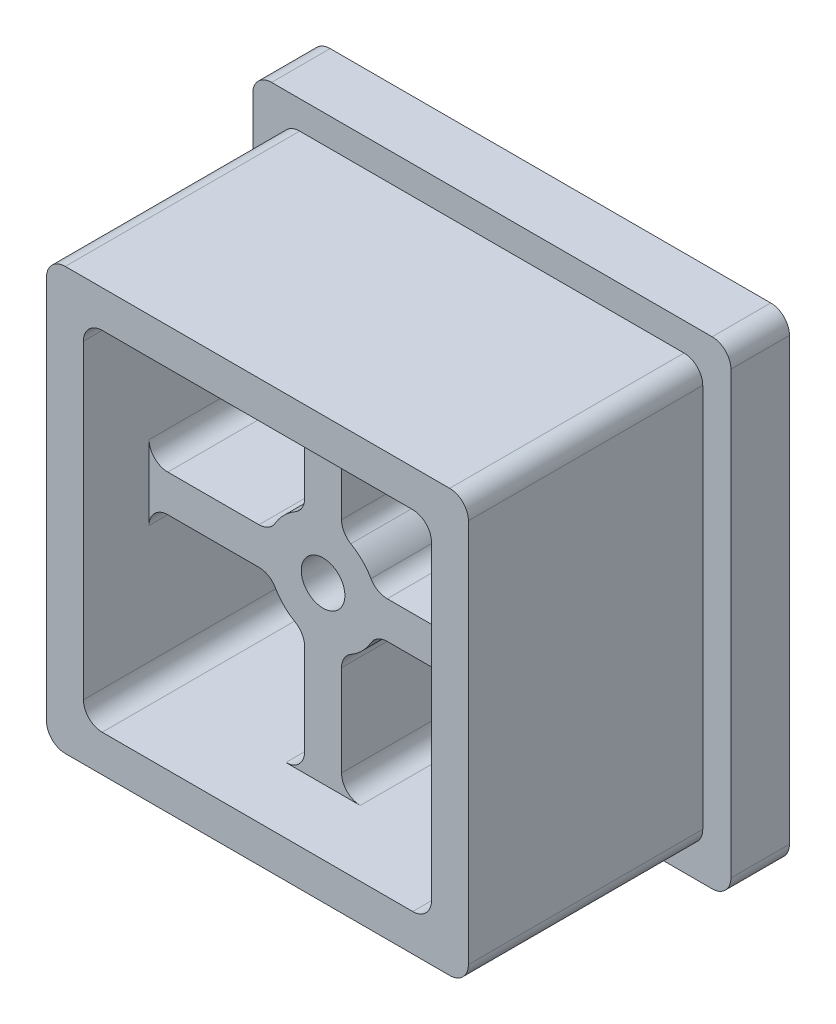
SolidWorks part; units mm, degrees
material "Nylon 101"
ref_plane "Front Plane" through (0, 0, 0) normal (0, 0, 1) x (1, 0, 0)
ref_plane "Top Plane" through (0, 0, 0) normal (0, 1, 0) x (1, 0, 0)
ref_plane "Right Plane" through (0, 0, 0) normal (1, 0, 0) x (0, 0, -1)
sketch "Sketch1" plane through (0, 0, 0) normal (0, 0, 1) x (1, 0, 0)
  line L1 (-5.715, 5.715) -> (5.715, 5.715)
  line L2 (-5.715, 5.715) -> (-5.715, -5.715)
  line L3 (-5.715, -5.715) -> (5.715, -5.715)
  line L4 (5.715, 5.715) -> (5.715, -5.715)
  line L5 (-5.715, 5.715) -> (5.715, -5.715) construction
  line L6 (-5.715, -5.715) -> (5.715, 5.715) construction
  point P0 (0, 0)
  dimension "D1" = 11.43
  dimension "D2" = 11.43
extrude "Boss-Extrude1" add sketch "Sketch1" along normal blind 4.7625 and the other way blind 1.5875
sketch "Sketch2" plane through (0, 0, -1.5875) normal (0, 0, -1) x (-1, 0, 0)
  line L0 (-6.477, 6.477) -> (-6.477, -6.477)
  line L1 (-6.477, -6.477) -> (6.477, -6.477)
  line L2 (6.477, -6.477) -> (6.477, 6.477)
  line L3 (6.477, 6.477) -> (-6.477, 6.477)
  line L4 (-5.715, 5.715) -> (-5.715, -5.715)
  line L5 (-5.715, -5.715) -> (5.715, -5.715)
  line L6 (5.715, -5.715) -> (5.715, 5.715)
  line L7 (5.715, 5.715) -> (-5.715, 5.715)
  line L8 (-5.715, 5.715) -> (-5.715, -5.715) construction
  line L9 (-5.715, -5.715) -> (5.715, -5.715) construction
  line L10 (5.715, -5.715) -> (5.715, 5.715) construction
  line L11 (5.715, 5.715) -> (-5.715, 5.715) construction
  dimension "D1" = 0
  dimension "D2" = 0.762
extrude "Boss-Extrude2" add sketch "Sketch2" along normal blind 1.5875
sketch "Sketch3" plane through (0, 0, 4.7625) normal (0, 0, 1) x (1, 0, 0)
  line L0 (5.207, -5.207) -> (5.207, 5.207)
  line L1 (5.207, 5.207) -> (-5.207, 5.207)
  line L2 (-5.207, 5.207) -> (-5.207, -5.207)
  line L3 (-5.207, -5.207) -> (5.207, -5.207)
  line L4 (5.715, -5.715) -> (5.715, 5.715)
  line L5 (5.715, 5.715) -> (-5.715, 5.715)
  line L6 (-5.715, 5.715) -> (-5.715, -5.715)
  line L7 (-5.715, -5.715) -> (5.715, -5.715)
  line L8 (5.715, -5.715) -> (5.715, 5.715) construction
  line L9 (5.715, 5.715) -> (-5.715, 5.715) construction
  line L10 (-5.715, 5.715) -> (-5.715, -5.715) construction
  line L11 (-5.715, -5.715) -> (5.715, -5.715) construction
  dimension "D1" = 0
  dimension "D2" = 0.508
extrude "Cut-Extrude1" [suppressed] cut sketch "Sketch3" against normal blind 1.8415
sketch "Sketch6" plane through (0, 0, -3.175) normal (0, 0, -1) x (-1, 0, 0)
  line L0 (-6.477, 6.477) -> (6.477, -6.477) construction
  line L2 (1.27, -1.27) -> (-1.27, -1.27)
  line L3 (1.27, -1.27) -> (1.27, 1.27)
  line L4 (1.27, 1.27) -> (-1.27, 1.27)
  line L5 (-1.27, -1.27) -> (-1.27, 1.27)
  line L6 (1.27, -1.27) -> (-1.27, 1.27) construction
  line L7 (1.27, 1.27) -> (-1.27, -1.27) construction
  point P4 (0, 0)
  dimension "D1" = 2.54
  dimension "D2" = 2.54
sketch "Sketch7" [suppressed] plane through (0, 0, 2.921) normal (0, 0, 1) x (1, 0, 0)
  line L0 (7.3025, 7.3025) -> (-7.3025, -7.3025) construction
  line L1 (4.445, -4.445) -> (-4.445, -4.445)
  line L2 (4.445, -4.445) -> (4.445, 4.445)
  line L3 (4.445, 4.445) -> (-4.445, 4.445)
  line L4 (-4.445, -4.445) -> (-4.445, 4.445)
  line L5 (4.445, -4.445) -> (-4.445, 4.445) construction
  line L6 (4.445, 4.445) -> (-4.445, -4.445) construction
  line L7 (-5.207, 5.207) -> (-5.207, -5.207) construction
  line L8 (5.207, 5.207) -> (-5.207, 5.207) construction
  point P0 (0, 0)
  dimension "D1" = 0.762
  dimension "D2" = 0.762
loft "Cut-Loft1" [suppressed] cut profiles "Sketch7", "Sketch6"
fillet "Fillet1" [suppressed] radius 0.508
sketch "Sketch8" [suppressed] plane through (0, 0, 0) normal (1, 0, 0) x (0, 0, -1)
  line L0 (-4.7625, -5.207) -> (-4.7625, -5.715) construction
  line L1 (-4.7625, -5.207) -> (1.5875, -5.207) construction
  line L2 (1.5875, -5.715) -> (-4.7625, -5.715) construction
  line L3 (-4.5085, -5.207) -> (-4.7625, -5.207)
  line L4 (-4.7625, -5.207) -> (-4.7625, -5.715) construction
  line L5 (-4.7625, -5.715) -> (-4.5085, -5.715)
  line L6 (-4.7625, -5.207) -> (-4.7879, -5.207)
  line L7 (-4.7879, -5.207) -> (-4.7879, -5.715)
  line L8 (-4.7879, -5.715) -> (-4.7625, -5.715)
  arc A0 (-4.5085, -5.207) -> (-4.5085, -5.715) centre (-4.5085, -5.461) ccw
  dimension "D1" = 0.0254
sketch "Sketch9" plane through (0, 0, 4.7625) normal (0, 0, 1) x (1, 0, 0)
  line L4 (5.715, 5.715) -> (-5.715, 5.715)
  line L5 (-5.715, 5.715) -> (-5.715, -5.715)
  line L6 (-5.715, -5.715) -> (5.715, -5.715)
  line L7 (5.715, -5.715) -> (5.715, 5.715)
  line L8 (5.715, 5.715) -> (-5.715, 5.715)
  line L9 (-5.715, 5.715) -> (-5.715, -5.715)
  line L10 (-5.715, -5.715) -> (5.715, -5.715)
  line L11 (5.715, -5.715) -> (5.715, 5.715)
  dimension "D1" = 0
sweep "Cut-Sweep2" [suppressed] cut profiles "Sketch8" path "Sketch9"
sketch "Sketch10" [suppressed] plane through (0, 0, 2.921) normal (0, 0, 1) x (1, 0, 0)
  line L0 (-4.3153, 3.8458) -> (-4.3153, -3.8458) construction
  line L1 (-4.3153, -3.8458) -> (-1.27, -0.8005) construction
  line L2 (-1.27, -0.8005) -> (-1.27, 0.8005) construction
  line L3 (-1.27, 0.8005) -> (-4.3153, 3.8458) construction
  line L4 (-0.8005, 1.27) -> (0.8005, 1.27) construction
  line L5 (0.8005, 1.27) -> (3.8458, 4.3153) construction
  line L6 (3.8458, 4.3153) -> (-3.8458, 4.3153) construction
  line L7 (-3.8458, 4.3153) -> (-0.8005, 1.27) construction
  line L8 (1.27, 0.8005) -> (1.27, -0.8005) construction
  line L9 (1.27, -0.8005) -> (4.3153, -3.8458) construction
  line L10 (4.3153, -3.8458) -> (4.3153, 3.8458) construction
  line L11 (4.3153, 3.8458) -> (1.27, 0.8005) construction
  line L12 (0.8005, -1.27) -> (-0.8005, -1.27) construction
  line L13 (-0.8005, -1.27) -> (-3.8458, -4.3153) construction
  line L14 (-3.8458, -4.3153) -> (3.8458, -4.3153) construction
  line L15 (3.8458, -4.3153) -> (0.8005, -1.27) construction
  line L16 (-4.3153, 3.8458) -> (-4.3153, -3.8458) construction
  line L17 (-4.3153, -3.8458) -> (-1.27, -0.8005) construction
  line L18 (-1.27, -0.8005) -> (-1.27, 0.8005) construction
  line L19 (-1.27, 0.8005) -> (-4.3153, 3.8458) construction
  line L20 (-0.8005, 1.27) -> (0.8005, 1.27) construction
  line L21 (0.8005, 1.27) -> (3.8458, 4.3153) construction
  line L22 (3.8458, 4.3153) -> (-3.8458, 4.3153) construction
  line L23 (-3.8458, 4.3153) -> (-0.8005, 1.27) construction
  line L24 (1.27, 0.8005) -> (1.27, -0.8005) construction
  line L25 (1.27, -0.8005) -> (4.3153, -3.8458) construction
  line L26 (4.3153, -3.8458) -> (4.3153, 3.8458) construction
  line L27 (4.3153, 3.8458) -> (1.27, 0.8005) construction
  line L28 (0.8005, -1.27) -> (-0.8005, -1.27) construction
  line L29 (-0.8005, -1.27) -> (-3.8458, -4.3153) construction
  line L30 (-3.8458, -4.3153) -> (3.8458, -4.3153) construction
  line L31 (3.8458, -4.3153) -> (0.8005, -1.27) construction
  line L32 (-3.5533, 2.0061) -> (-3.5533, -2.0061)
  line L33 (-3.5533, -2.0061) -> (-2.032, -0.4849)
  line L34 (-2.032, -0.4849) -> (-2.032, 0.4849)
  line L35 (-2.032, 0.4849) -> (-3.5533, 2.0061)
  line L36 (-0.4849, 2.032) -> (0.4849, 2.032)
  line L37 (0.4849, 2.032) -> (2.0061, 3.5533)
  line L38 (2.0061, 3.5533) -> (-2.0061, 3.5533)
  line L39 (-2.0061, 3.5533) -> (-0.4849, 2.032)
  line L40 (2.032, 0.4849) -> (2.032, -0.4849)
  line L41 (2.032, -0.4849) -> (3.5533, -2.0061)
  line L42 (3.5533, -2.0061) -> (3.5533, 2.0061)
  line L43 (3.5533, 2.0061) -> (2.032, 0.4849)
  line L44 (0.4849, -2.032) -> (-0.4849, -2.032)
  line L45 (-0.4849, -2.032) -> (-2.0061, -3.5533)
  line L46 (-2.0061, -3.5533) -> (2.0061, -3.5533)
  line L47 (2.0061, -3.5533) -> (0.4849, -2.032)
  dimension "D1" = 0.762
extrude "Cut-Extrude2" [suppressed] cut sketch "Sketch10" against normal offset from surface (6.4135 mm away) 1.27
fillet "Fillet4" [suppressed] radius 0.254
fillet "Fillet5" [suppressed] radius 0.254
sketch "Sketch11" [suppressed] plane through (0, 0, 2.921) normal (0, 0, 1) x (1, 0, 0)
  line L1 (2.54, -2.54) -> (-2.54, -2.54)
  line L2 (2.54, -2.54) -> (2.54, 2.54)
  line L3 (2.54, 2.54) -> (-2.54, 2.54)
  line L4 (-2.54, -2.54) -> (-2.54, 2.54)
  line L5 (2.54, -2.54) -> (-2.54, 2.54) construction
  line L6 (2.54, 2.54) -> (-2.54, -2.54) construction
  point P0 (0, 0)
  dimension "D1" = 5.08
  dimension "D2" = 5.08
extrude "Cut-Extrude3" [suppressed] cut sketch "Sketch11" against normal through all draft 5
sketch "Sketch12" [suppressed] plane through (0, 0, 2.921) normal (0, 0, 1) x (1, 0, 0)
  line L0 (-5.207, 0) -> (5.207, 0)
  line L1 (-5.207, 5.207) -> (-5.207, -5.207) construction
  line L2 (5.207, -5.207) -> (5.207, 5.207) construction
  line L3 (0, 5.207) -> (0, -5.207)
  line L4 (5.207, 5.207) -> (-5.207, 5.207) construction
  line L5 (-5.207, -5.207) -> (5.207, -5.207) construction
extrude "Cut-Extrude-Thin1" [suppressed] cut sketch "Sketch12" against normal offset from surface (6.4135 mm away) 1.27 thin
fillet "Fillet6" [suppressed] radius 0.508
sketch "Sketch13" [suppressed] plane through (0, 0, 0) normal (1, 0, 0) x (0, 0, -1)
  line L0 (1.5875, -5.715) -> (-4.7625, -5.715) construction
  line L1 (-2.921, -5.207) -> (-4.7625, -5.207) construction
  line L2 (-4.7625, -5.715) -> (-4.7625, 5.715) construction
  line L3 (-4.5085, -5.207) -> (-5.0165, -5.207)
  line L4 (-5.0165, -5.207) -> (-5.0165, -5.715)
  line L5 (-5.0165, -5.715) -> (-4.5085, -5.715)
  arc A0 (-4.5085, -5.207) -> (-4.5085, -5.715) centre (-4.5085, -5.461) ccw
  dimension "D1" = 0.508
sketch "Sketch14" plane through (0, 0, 4.7625) normal (0, 0, 1) x (1, 0, 0)
  line L4 (5.715, -5.715) -> (5.715, 5.715)
  line L5 (5.715, 5.715) -> (-5.715, 5.715)
  line L6 (-5.715, 5.715) -> (-5.715, -5.715)
  line L7 (-5.715, -5.715) -> (5.715, -5.715)
  line L8 (5.715, -5.715) -> (5.715, 5.715)
  line L9 (5.715, 5.715) -> (-5.715, 5.715)
  line L10 (-5.715, 5.715) -> (-5.715, -5.715)
  line L11 (-5.715, -5.715) -> (5.715, -5.715)
  dimension "D1" = 0
sweep "Cut-Sweep3" [suppressed] cut profiles "Sketch13" path "Sketch14"
shell "Shell1" thickness 1
sketch "Sketch15" plane through (0, 0, -3.175) normal (0, 0, -1) x (-1, 0, 0)
  circle A0 centre (0, 0) radius 1.5
  dimension "D1" = 3
extrude "Boss-Extrude3" add sketch "Sketch15" against normal offset from surface (6.1595 mm away) 1.778 separate body up to face at (0, 0, 4.7625)
sketch "Sketch16" plane through (0, 0, 2.9845) normal (0, 0, 1) x (1, 0, 0)
  line L0 (0, 4.715) -> (0, -4.715)
  line L1 (4.715, 4.715) -> (-4.715, 4.715) construction
  line L2 (-4.715, -4.715) -> (4.715, -4.715) construction
  line L4 (4.715, -4.715) -> (4.715, 4.715) construction
  line L5 (4.715, 0) -> (-4.715, 0)
  line L6 (-4.715, 4.715) -> (-4.715, -4.715) construction
extrude "Extrude-Thin1" add sketch "Sketch16" against normal up to surface (6.1595 mm away) thin up to face at (0, 0, -3.175) thin type mid plane wall 1
sketch "Sketch17" plane through (0, 0, -3.175) normal (0, 0, -1) x (-1, 0, 0)
  line L1 (4.715, 4.715) -> (-4.715, 4.715)
  line L2 (-4.715, 4.715) -> (-4.715, -4.715)
  line L3 (-4.715, -4.715) -> (4.715, -4.715)
  line L4 (4.715, -4.715) -> (4.715, 4.715)
  line L5 (5.477, 5.477) -> (-5.477, 5.477)
  line L6 (-5.477, 5.477) -> (-5.477, -5.477)
  line L8 (-5.477, -5.477) -> (5.477, -5.477)
  line L9 (5.477, -5.477) -> (5.477, 5.477)
  line L10 (5.477, 5.477) -> (-5.477, 5.477)
  line L11 (-5.477, 5.477) -> (-5.477, -5.477)
  line L12 (-5.477, -5.477) -> (5.477, -5.477)
  line L13 (5.477, -5.477) -> (5.477, 5.477)
  dimension "D1" = 0
  dimension "D2" = 0.762
extrude "Boss-Extrude4" add sketch "Sketch17" against normal up to next
sketch "Sketch18" plane through (0, 0, 2.9845) normal (0, 0, 1) x (1, 0, 0)
  circle A0 centre (0, 0) radius 0.5
  arc A3 (0.5, -1.4142) -> (1.4142, -0.5) centre (0, 0) ccw construction
  dimension "D1" = 1
extrude "Cut-Extrude4" [suppressed] cut sketch "Sketch18" against normal through all
fillet "Fillet7" radius 0.508 8 edges at (-6.477, -6.477, -2.3812) (-5.715, -5.715, 1.5875) (5.715, -5.715, 1.5875) (6.477, -6.477, -2.3812) (5.715, 5.715, 1.5875) (6.477, 6.477, -2.3812) (-6.477, 6.477, -2.3812) (-5.715, 5.715, 1.5875)
fillet "Fillet8" radius 0.508 20 edges at (-4.715, -4.715, 0.7938) (-4.715, 4.715, 0.7938) (4.715, 4.715, 0.7938) (4.715, -4.715, 0.7938) (-0.5, 4.715, -0.0952) (0.5, 4.715, -0.0952) (4.715, 0.5, -0.0952) (4.715, -0.5, -0.0953) (0.5, -4.715, -0.0952) (-0.5, -4.715, -0.0952) (-4.715, -0.5, -0.0952) (-4.715, 0.5, -0.0952) (1.4142, -0.5, -0.0952) (-1.4142, -0.5, -0.0953) (-0.5, -1.4142, -0.0953) (-0.5, 1.4142, -0.0953) (0.5, -1.4142, -0.0952) (0.5, 1.4142, -0.0952) (1.4142, 0.5, -0.0953) (-1.4142, 0.5, -0.0952)
sketch "Sketch20" plane through (0, 0, -3.175) normal (0, 0, -1) x (-1, 0, 0)
  circle A0 centre (0, 0) radius 0.635
  dimension "D1" = 1.27
split line "Split Line1" [suppressed]
dome "Dome2" [suppressed] faces to dome 1 distance 0.635 parameters "D1"=0.635
hole_wizard "#56 (0.0465) Diameter Hole1" positions "Sketch22" profile "Sketch21" hole size "#56" standard "ANSI Inch" end condition through all
sketch "Sketch22" plane through (0, 0, 2.9845) normal (0, 0, 1) x (1, 0, 0)
  point P0 (0, 0)
sketch "Sketch21" plane through (0, 0, 2.9845) normal (1, 0, 0) x (0, -1, 0)
  line L0 (0, 0) -> (0, 6.1595)
  line L1 (0, 6.1595) -> (0.5905, 6.1595)
  line L2 (0.5905, 6.1595) -> (0.5905, 0)
  line L5 (0.5905, 0) -> (0, 0)
  line L11 (0, -6.35) -> (0, 107.95) construction
  dimension "Thru Hole Dia." = 1.1811
  dimension "Thru Hole Depth" = 6.1595
equation "\"D2@Sketch7\"=\"D1@Sketch7\""
